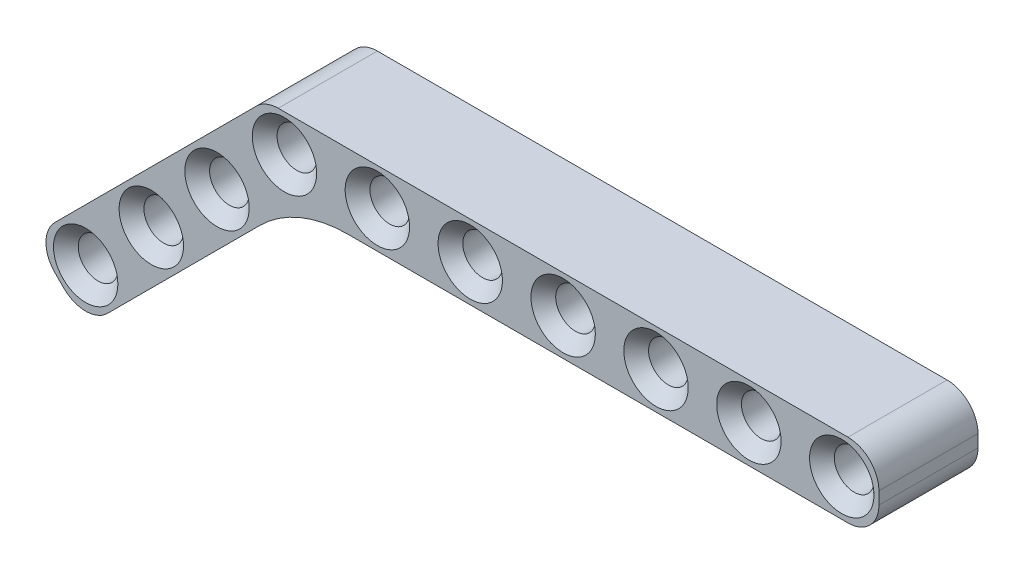
SolidWorks part; units mm, degrees
ref_plane "Front Plane" through (0, 0, 0) normal (0, 0, 1) x (1, 0, 0)
ref_plane "Top Plane" through (0, 0, 0) normal (0, 1, 0) x (1, 0, 0)
ref_plane "Right Plane" through (0, 0, 0) normal (1, 0, 0) x (0, 0, -1)
sketch "Sketch1" plane through (0, 0, 0) normal (0, 0, 1) x (1, 0, 0)
  line L1 (-0.5, 3) -> (45.5, 3)
  line L2 (-3, 0.5) -> (-3, -0.5)
  line L3 (-0.5, -3) -> (45.5, -3)
  line L4 (48, 0.5) -> (48, -0.5)
  circle A0 centre (0, 0) radius 1.6
  arc A1 (45.5, -3) -> (48, -0.5) centre (45.5, -0.5) ccw
  arc A2 (45.5, 3) -> (48, 0.5) centre (45.5, 0.5) cw
  arc A3 (-3, -0.5) -> (-0.5, -3) centre (-0.5, -0.5) ccw
  arc A4 (-0.5, 3) -> (-3, 0.5) centre (-0.5, 0.5) ccw
  circle A5 centre (7.5, 0) radius 1.6
  circle A6 centre (15, 0) radius 1.6
  circle A7 centre (22.5, 0) radius 1.6
  circle A8 centre (30, 0) radius 1.6
  circle A9 centre (37.5, 0) radius 1.6
  circle A10 centre (45, 0) radius 1.6
  point P8 (-3, 0)
  point P14 (-3, -3)
  point P17 (-3, 3)
  dimension "D1" = 3.2
  dimension "D4" = 2.5
  dimension "D2" = 6
  dimension "D3" = 3
  dimension "D6" = 7.5
  dimension "D5" = 7
extrude "Boss-Extrude1" add sketch "Sketch1" along normal blind 8
chamfer "Chamfer1" distance 1 angle 45 10 edges at (31.6, 0, 0) (31.6, 0, 8) (24.1, 0, 0) (24.1, 0, 8) (16.6, 0, 0) (16.6, 0, 8) (9.1, 0, 0) (9.1, 0, 8) (1.6, 0, 0) (1.6, 0, 8)
sketch "Sketch2" plane through (0, 0, 8) normal (0, 0, 1) x (1, 0, 0)
  line L0 (-2.2678, 2.2678) -> (-18.5292, -13.9937)
  line L1 (-18.5292, -17.5292) -> (-17.8221, -18.2363)
  line L2 (-14.2866, -18.2363) -> (0.9497, -3)
  line L4 (-0.5, -3) -> (45.5, -3) construction
  arc A0 (-0.5, 3) -> (-3, 0.5) centre (-0.5, 0.5) ccw construction
  circle A1 centre (-5.4477, -5.1548) radius 1.6
  circle A2 centre (-10.751, -10.4581) radius 1.6
  circle A3 centre (-16.0543, -15.7614) radius 1.6
  arc A4 (-18.5292, -13.9937) -> (-18.5292, -17.5292) centre (-16.7614, -15.7614) ccw
  arc A5 (-17.8221, -18.2363) -> (-14.2866, -18.2363) centre (-16.0543, -16.4685) ccw
  point P18 (-20.297, -15.7614)
  point P21 (-16.0543, -20.0041)
  arc M15 (-0.5, 3) -> (-3, 0.5) centre (-0.5, 0.5) ccw
  line M16 (-3, 0.5) -> (-3, -0.5)
  arc M17 (-3, -0.5) -> (-0.5, -3) centre (-0.5, -0.5) ccw
  line M18 (-0.5, -3) -> (45.5, -3)
  dimension "D3" = 3.2
  dimension "D8" = 2.5
  dimension "D1" = 6
  dimension "D2" = 45
  dimension "D4" = 3
  dimension "D5" = 7.5
  dimension "D7" = 3
  dimension "D6" = 3
extrude "Boss-Extrude3" add sketch "Sketch2" against normal blind 8 contours L1 A5 L2 L0 A4 A1 A2 A3 M18 M17 M16 M15
fillet "Fillet1" radius 10 1 edges at (0.9497, -3, 4)
chamfer "Chamfer2" distance 1 angle 45 6 edges at (-14.4543, -15.7614, 8) (-14.4543, -15.7614, 0) (-9.151, -10.4581, 8) (-9.151, -10.4581, 0) (-3.8477, -5.1548, 8) (-3.8477, -5.1548, 0)
chamfer "Chamfer3" distance 1 angle 45 4 edges at (46.6, 0, 0) (46.6, 0, 8) (39.1, 0, 0) (39.1, 0, 8)
